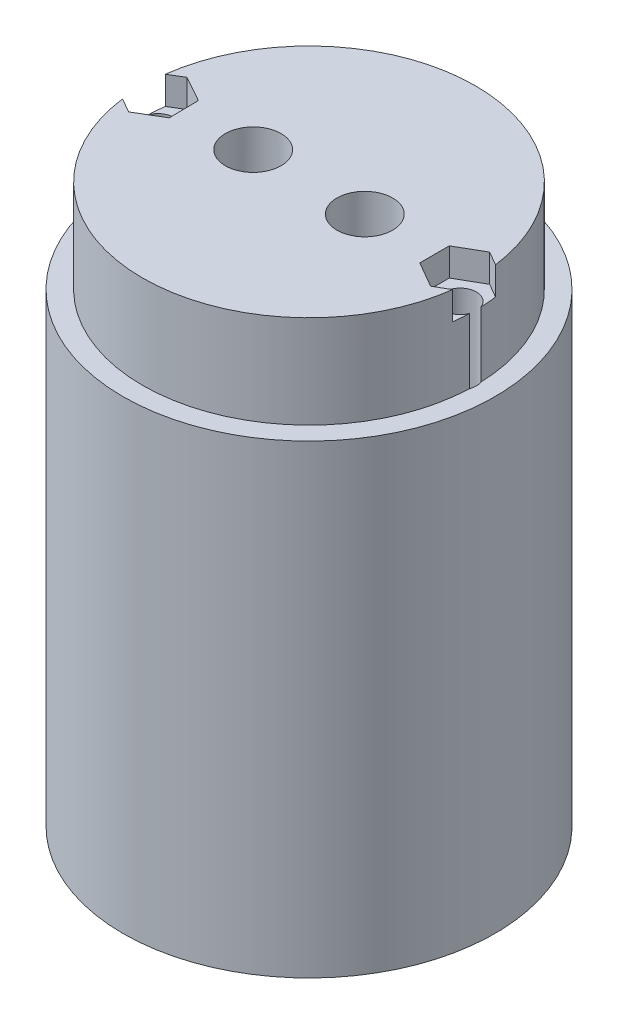
SolidWorks part; units mm, degrees
ref_plane "Front Plane" through (0, 0, 0) normal (0, 0, 1) x (1, 0, 0)
ref_plane "Top Plane" through (0, 0, 0) normal (0, 1, 0) x (1, 0, 0)
ref_plane "Right Plane" through (0, 0, 0) normal (1, 0, 0) x (0, 0, -1)
sketch "Sketch1" plane through (0, 13.6944, 0) normal (0, -1, 0) x (-1, 0, 0)
  circle A0 centre (-0.536, -73.6008) radius 18
  circle A1 centre (-0.536, -73.6008) radius 17.9
  circle A2 centre (-0.536, -73.6008) radius 18 construction
  dimension "D1" = 0.1
extrude "Boss-Extrude1" add sketch "Sketch1" along normal blind 10 contours A1
sketch "Sketch2" plane through (0, 3.6944, 0) normal (0, -1, 0) x (-1, 0, 0)
  circle A0 centre (-0.536, -73.6008) radius 20
extrude "Boss-Extrude2" add sketch "Sketch2" along normal blind 40
sketch "Sketch3" plane through (0, 81.6944, 0) normal (0, 1, 0) x (1, 0, 0)
  circle A0 centre (-15.714, -73.6008) radius 1.75
  circle A1 centre (16.786, -73.6008) radius 1.75
extrude "Cut-Extrude1" cut sketch "Sketch3" against normal through all both and the other way through all
sketch "Sketch4" plane through (0, 13.6944, 0) normal (0, 1, 0) x (1, 0, 0)
  line L1 (-15.7599, -70.4257) -> (-18.4867, -72.0531)
  line L2 (-18.4867, -72.0531) -> (-18.4407, -75.2282)
  line L3 (-18.4407, -75.2282) -> (-15.6681, -76.7759)
  line L4 (-15.6681, -76.7759) -> (-12.9413, -75.1486)
  line L5 (-12.9413, -75.1486) -> (-12.9873, -71.9735)
  line L6 (-12.9873, -71.9735) -> (-15.7599, -70.4257)
  line L7 (16.786, -70.4254) -> (14.036, -72.0131)
  line L8 (14.036, -72.0131) -> (14.036, -75.1885)
  line L9 (14.036, -75.1885) -> (16.786, -76.7762)
  line L10 (16.786, -76.7762) -> (19.536, -75.1885)
  line L11 (19.536, -75.1885) -> (19.536, -72.0131)
  line L12 (19.536, -72.0131) -> (16.786, -70.4254)
  circle A0 centre (-15.714, -73.6008) radius 2.75 construction
  circle A1 centre (16.786, -73.6008) radius 2.75 construction
  dimension "D1" = 5.5
extrude "Cut-Extrude2" cut sketch "Sketch4" against normal blind 3
sketch "Sketch5" plane through (0, 13.6944, 0) normal (0, 1, 0) x (1, 0, 0)
  circle A0 centre (0.536, -73.6008) radius 12
  dimension "D1" = 24
extrude "Cut-Extrude4" cut sketch "Sketch5" against normal blind 43 from offset 10 offset against normal yes
fillet "Fillet1" radius 10 1 edges at (0.536, 3.6944, 85.6008)
sketch "Sketch6" plane through (0, -36.3056, 0) normal (0, -1, 0) x (1, 0, 0)
  circle A0 centre (0.536, 73.6008) radius 20
  circle A1 centre (0.536, 73.6008) radius 18
  dimension "D1" = 36
extrude "Boss-Extrude3" add sketch "Sketch6" along normal blind 10
sketch "Sketch7" plane through (0, -36.3056, 0) normal (0, -1, 0) x (-1, 0, 0)
  circle A0 centre (-0.536, -73.6008) radius 13
  dimension "D1" = 26
extrude "Cut-Extrude5" cut sketch "Sketch7" against normal blind 40 contours A0
fillet "Fillet2" radius 10 1 edges at (0.536, 3.6944, 60.6008)
sketch "Sketch8" plane through (0, -36.3056, 0) normal (0, -1, 0) x (-1, 0, 0)
  line L0 (12.464, -73.6008) -> (-13.536, -73.6008)
  line L1 (-0.536, -73.6008) -> (-0.536, -77.486)
  line L2 (-0.536, -77.486) -> (-6.536, -73.6008)
  line L3 (-6.536, -73.6008) -> (5.464, -73.6008)
  line L4 (5.464, -73.6008) -> (-0.536, -77.486)
  circle A0 centre (-0.536, -73.6008) radius 13 construction
  circle A1 centre (-0.536, -73.6008) radius 13 construction
  circle A2 centre (5.464, -73.6008) radius 3
  circle A3 centre (-6.536, -73.6008) radius 3
  dimension "D1" = 6
  dimension "D2" = 6
extrude "Cut-Extrude6" cut sketch "Sketch8" against normal through all both and the other way through all contours L4 A2 L0 | L0 A2 | L0 A2 L4 | L0 A3 L2 | L2 A3 L3 | L3 A3 L0
sketch "Sketch10" plane through (0, -36.3056, 0) normal (0, -1, 0) x (-1, 0, 0)
  circle A1 centre (-0.536, -73.6008) radius 14
  dimension "D1" = 28
extrude "Cut-Extrude7" cut sketch "Sketch10" against normal blind 15
